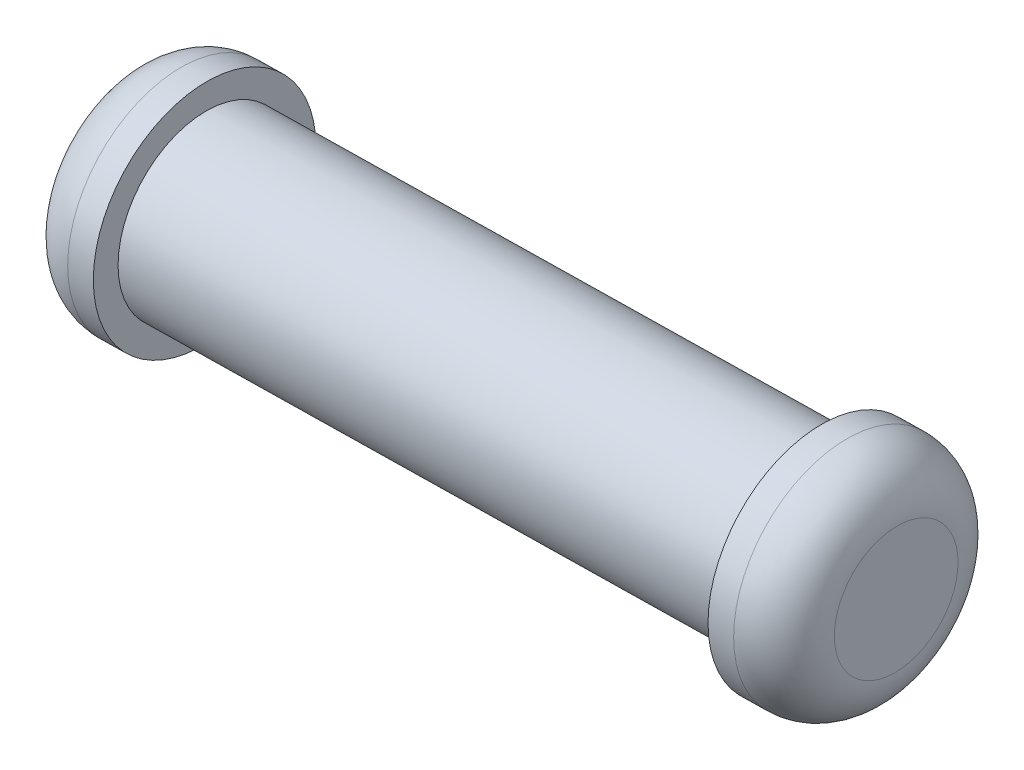
SolidWorks part; units mm, degrees
material "Plain Carbon Steel"
ref_plane "Front Plane" through (0, 0, 0) normal (0, 0, 1) x (1, 0, 0)
ref_plane "Top Plane" through (0, 0, 0) normal (0, 1, 0) x (1, 0, 0)
ref_plane "Right Plane" through (0, 0, 0) normal (1, 0, 0) x (0, 0, -1)
sketch "Sketch1" plane through (-50.0411, 0, 0.8661) normal (-0.9999, 0, 0.0173) x (0.0173, 0, 0.9999)
  circle A0 centre (-1.2936, 26.7347) radius 1.75
extrude "Boss-Extrude1" add sketch "Sketch1" against normal up to surface (12 mm away)
sketch "Sketch2" plane through (-50.0411, 0, 0.8661) normal (-0.9999, 0, 0.0173) x (0.0173, 0, 0.9999)
  circle A0 centre (-1.2936, 26.7347) radius 2.25
  dimension "D1" = 4.5
extrude "Boss-Extrude2" add sketch "Sketch2" along normal blind 1.5
sketch "Sketch3" plane through (-38.0429, 0, 0.6584) normal (0.9999, 0, -0.0173) x (-0.0173, 0, -0.9999)
  circle A0 centre (1.2936, 26.7347) radius 2.25
extrude "Boss-Extrude3" add sketch "Sketch3" along normal blind 1.5
fillet "Fillet1" radius 1 2 edges at (-51.5244, 26.7347, 1.8483) (-36.6045, 26.7347, -2.9106)
